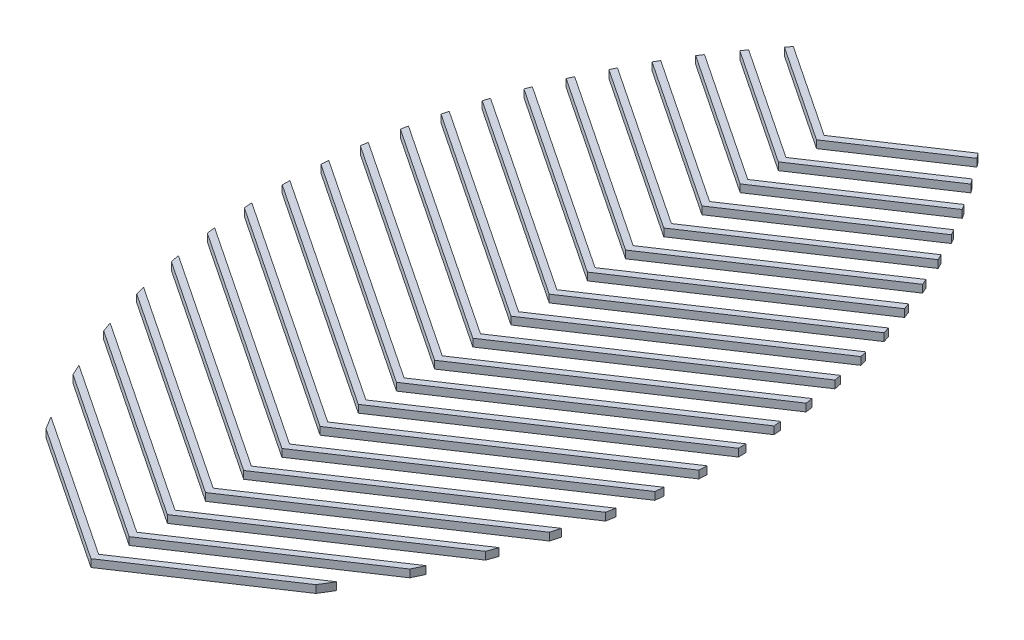
SolidWorks part; units mm, degrees
ref_plane "Front Plane" through (0, 0, 0) normal (0, 0, 1) x (1, 0, 0)
ref_plane "Top Plane" through (0, 0, 0) normal (0, 1, 0) x (1, 0, 0)
ref_plane "Right Plane" through (0, 0, 0) normal (1, 0, 0) x (0, 0, -1)
sketch "Sketch2" plane through (0, 0, 0) normal (0, 1, 0) x (1, 0, 0)
  line L0 (-15.0876, 6.8922) -> (8.6636, -8.942)
  line L1 (8.6636, -8.942) -> (32.4148, 6.8922)
  line L2 (-20.2008, 16.651) -> (8.6636, -2.592)
  line L3 (8.6636, -3.862) -> (8.6636, -8.942) construction
  line L4 (-13.7712, 4.7445) -> (8.6636, -10.212)
  line L5 (8.6636, -10.212) -> (31.0984, 4.7445)
  line L7 (8.6636, -8.942) -> (8.6636, -10.212) construction
  line L9 (8.6636, -2.592) -> (37.5281, 16.651)
  line L10 (-19.336, 14.8045) -> (8.6636, -3.862)
  line L11 (8.6636, -3.862) -> (36.6632, 14.8045)
  line L14 (8.6636, 2.488) -> (8.6636, -2.592) construction
  line L15 (8.6636, -2.592) -> (8.6636, -3.862) construction
  line L16 (-23.6775, 25.3188) -> (8.6636, 3.758)
  line L17 (8.6636, 3.758) -> (41.0047, 25.3188)
  line L18 (-23.0802, 23.6506) -> (8.6636, 2.488)
  line L19 (8.6636, 2.488) -> (40.4074, 23.6506)
  line L22 (8.6636, 8.838) -> (8.6636, 3.758) construction
  line L23 (8.6636, 3.758) -> (8.6636, 2.488) construction
  line L24 (-26.0837, 33.2729) -> (8.6636, 10.108)
  line L25 (8.6636, 10.108) -> (43.4109, 33.2729)
  line L26 (-25.6722, 31.7286) -> (8.6636, 8.838)
  line L27 (8.6636, 8.838) -> (42.9994, 31.7286)
  line L30 (8.6636, 15.188) -> (8.6636, 10.108) construction
  line L31 (8.6636, 10.108) -> (8.6636, 8.838) construction
  line L32 (-27.7036, 40.7028) -> (8.6636, 16.458)
  line L33 (8.6636, 16.458) -> (45.0308, 40.7028)
  line L34 (-27.4334, 39.2527) -> (8.6636, 15.188)
  line L35 (8.6636, 15.188) -> (44.7606, 39.2527)
  line L38 (8.6636, 21.538) -> (8.6636, 16.458) construction
  line L39 (8.6636, 16.458) -> (8.6636, 15.188) construction
  line L40 (-28.7043, 47.72) -> (8.6636, 22.808)
  line L41 (8.6636, 22.808) -> (46.0315, 47.72)
  line L42 (-28.5479, 46.3457) -> (8.6636, 21.538)
  line L43 (8.6636, 21.538) -> (45.8752, 46.3457)
  line L46 (8.6636, 27.888) -> (8.6636, 22.808) construction
  line L47 (8.6636, 22.808) -> (8.6636, 21.538) construction
  line L48 (-29.1937, 54.3963) -> (8.6636, 29.158)
  line L49 (8.6636, 29.158) -> (46.5209, 54.3963)
  line L50 (-29.1328, 53.0857) -> (8.6636, 27.888)
  line L51 (8.6636, 27.888) -> (46.4601, 53.0857)
  line L54 (8.6636, 34.238) -> (8.6636, 29.158) construction
  line L55 (8.6636, 29.158) -> (8.6636, 27.888) construction
  line L56 (-29.246, 60.7811) -> (8.6636, 35.508)
  line L57 (8.6636, 35.508) -> (46.5732, 60.7811)
  line L58 (-29.2677, 59.5256) -> (8.6636, 34.238)
  line L59 (8.6636, 34.238) -> (46.5949, 59.5256)
  line L62 (8.6636, 40.588) -> (8.6636, 35.508) construction
  line L63 (8.6636, 35.508) -> (8.6636, 34.238) construction
  line L64 (-28.9145, 66.9101) -> (8.6636, 41.858)
  line L65 (8.6636, 41.858) -> (46.2417, 66.9101)
  line L66 (-29.0094, 65.7034) -> (8.6636, 40.588)
  line L67 (8.6636, 40.588) -> (46.3367, 65.7034)
  line L70 (8.6636, 46.938) -> (8.6636, 41.858) construction
  line L71 (8.6636, 41.858) -> (8.6636, 40.588) construction
  line L72 (-28.2388, 72.8096) -> (8.6636, 48.208)
  line L73 (8.6636, 48.208) -> (45.566, 72.8096)
  line L74 (-28.3999, 71.647) -> (8.6636, 46.938)
  line L75 (8.6636, 46.938) -> (45.7271, 71.647)
  line L78 (8.6636, 53.288) -> (8.6636, 48.208) construction
  line L79 (8.6636, 48.208) -> (8.6636, 46.938) construction
  line L80 (-27.2489, 78.4997) -> (8.6636, 54.558)
  line L81 (8.6636, 54.558) -> (44.5761, 78.4997)
  line L82 (-27.4708, 77.3777) -> (8.6636, 53.288)
  line L83 (8.6636, 53.288) -> (44.798, 77.3777)
  line L86 (8.6636, 59.638) -> (8.6636, 54.558) construction
  line L87 (8.6636, 54.558) -> (8.6636, 53.288) construction
  line L88 (-25.968, 83.9958) -> (8.6636, 60.908)
  line L89 (8.6636, 60.908) -> (43.2952, 83.9958)
  line L90 (-26.2465, 82.9115) -> (8.6636, 59.638)
  line L91 (8.6636, 59.638) -> (43.5737, 82.9115)
  line L94 (8.6636, 65.988) -> (8.6636, 60.908) construction
  line L95 (8.6636, 60.908) -> (8.6636, 59.638) construction
  line L96 (-24.4139, 89.3097) -> (8.6636, 67.258)
  line L97 (8.6636, 67.258) -> (41.7411, 89.3097)
  line L98 (-24.7458, 88.261) -> (8.6636, 65.988)
  line L99 (8.6636, 65.988) -> (42.073, 88.261)
  line L102 (8.6636, 72.338) -> (8.6636, 67.258) construction
  line L103 (8.6636, 67.258) -> (8.6636, 65.988) construction
  line L104 (-22.6004, 94.4507) -> (8.6636, 73.608)
  line L105 (8.6636, 73.608) -> (39.9276, 94.4507)
  line L106 (-22.9833, 93.436) -> (8.6636, 72.338)
  line L107 (8.6636, 72.338) -> (40.3105, 93.436)
  line L110 (8.6636, 78.688) -> (8.6636, 73.608) construction
  line L111 (8.6636, 73.608) -> (8.6636, 72.338) construction
  line L112 (-20.5381, 99.4258) -> (8.6636, 79.958)
  line L113 (8.6636, 79.958) -> (37.8653, 99.4258)
  line L114 (-20.9701, 98.4438) -> (8.6636, 78.688)
  line L115 (8.6636, 78.688) -> (38.2973, 98.4438)
  line L118 (8.6636, 85.038) -> (8.6636, 79.958) construction
  line L119 (8.6636, 79.958) -> (8.6636, 78.688) construction
  line L120 (-18.2347, 104.2403) -> (8.6636, 86.308)
  line L121 (8.6636, 86.308) -> (35.562, 104.2403)
  line L122 (-18.7144, 103.29) -> (8.6636, 85.038)
  line L123 (8.6636, 85.038) -> (36.0416, 103.29)
  line L126 (8.6636, 91.388) -> (8.6636, 86.308) construction
  line L127 (8.6636, 86.308) -> (8.6636, 85.038) construction
  line L128 (-15.6958, 108.8976) -> (8.6636, 92.658)
  line L129 (8.6636, 92.658) -> (33.023, 108.8976)
  line L130 (-16.2222, 107.9786) -> (8.6636, 91.388)
  line L131 (8.6636, 91.388) -> (33.5494, 107.9786)
  line L134 (8.6636, 97.738) -> (8.6636, 92.658) construction
  line L135 (8.6636, 92.658) -> (8.6636, 91.388) construction
  line L136 (-12.9245, 113.4001) -> (8.6636, 99.008)
  line L137 (8.6636, 99.008) -> (30.2517, 113.4001)
  line L138 (-13.4973, 112.512) -> (8.6636, 97.738)
  line L139 (8.6636, 97.738) -> (30.8245, 112.512)
  line L142 (8.6636, 104.088) -> (8.6636, 99.008) construction
  line L143 (8.6636, 99.008) -> (8.6636, 97.738) construction
  line L144 (-9.9223, 117.7486) -> (8.6636, 105.358)
  line L145 (8.6636, 105.358) -> (27.2495, 117.7486)
  line L146 (-10.5412, 116.8912) -> (8.6636, 104.088)
  line L147 (8.6636, 104.088) -> (27.8684, 116.8912)
  line L150 (8.6636, 110.438) -> (8.6636, 105.358) construction
  line L151 (8.6636, 105.358) -> (8.6636, 104.088) construction
  line L152 (-6.6885, 121.9428) -> (8.6636, 111.708)
  line L153 (8.6636, 111.708) -> (24.0157, 121.9428)
  line L154 (-7.3538, 121.1163) -> (8.6636, 110.438)
  line L155 (8.6636, 110.438) -> (24.6811, 121.1163)
  line L158 (8.6636, 116.788) -> (8.6636, 111.708) construction
  line L159 (8.6636, 111.708) -> (8.6636, 110.438) construction
  arc A0 (-6.6885, 121.9428) -> (-7.3538, 121.1163) centre (71.3713, 58.4122) ccw
  arc A1 (24.0157, 121.9428) -> (24.6811, 121.1163) centre (-54.0441, 58.4122) cw
  arc A2 (32.4148, 6.8922) -> (31.0984, 4.7445) centre (-54.0441, 58.4122) cw
  arc A3 (37.5281, 16.651) -> (36.6632, 14.8045) centre (-54.0441, 58.4122) cw
  arc A4 (41.0047, 25.3188) -> (40.4074, 23.6506) centre (-54.0441, 58.4122) cw
  arc A5 (43.4109, 33.2729) -> (42.9994, 31.7286) centre (-54.0441, 58.4122) cw
  arc A6 (45.0308, 40.7028) -> (44.7606, 39.2527) centre (-54.0441, 58.4122) cw
  arc A7 (46.0315, 47.72) -> (45.8752, 46.3457) centre (-54.0441, 58.4122) cw
  arc A8 (46.5209, 54.3963) -> (46.4601, 53.0857) centre (-54.0441, 58.4122) cw
  arc A9 (46.5732, 60.7811) -> (46.5949, 59.5256) centre (-54.0441, 58.4122) cw
  arc A10 (46.2417, 66.9101) -> (46.3367, 65.7034) centre (-54.0441, 58.4122) cw
  arc A11 (45.566, 72.8096) -> (45.7271, 71.647) centre (-54.0441, 58.4122) cw
  arc A12 (44.5761, 78.4997) -> (44.798, 77.3777) centre (-54.0441, 58.4122) cw
  arc A13 (43.2952, 83.9958) -> (43.5737, 82.9115) centre (-54.0441, 58.4122) cw
  arc A14 (41.7411, 89.3097) -> (42.073, 88.261) centre (-54.0441, 58.4122) cw
  arc A15 (39.9276, 94.4507) -> (40.3105, 93.436) centre (-54.0441, 58.4122) cw
  arc A16 (37.8653, 99.4258) -> (38.2973, 98.4438) centre (-54.0441, 58.4122) cw
  arc A17 (35.562, 104.2403) -> (36.0416, 103.29) centre (-54.0441, 58.4122) cw
  arc A18 (33.023, 108.8976) -> (33.5494, 107.9786) centre (-54.0441, 58.4122) cw
  arc A19 (30.2517, 113.4001) -> (30.8245, 112.512) centre (-54.0441, 58.4122) cw
  arc A20 (27.2495, 117.7486) -> (27.8684, 116.8912) centre (-54.0441, 58.4122) cw
  arc A21 (-15.0876, 6.8922) -> (-13.7712, 4.7445) centre (71.3713, 58.4122) ccw
  arc A22 (-23.6775, 25.3188) -> (-23.0802, 23.6506) centre (71.3713, 58.4122) ccw
  arc A23 (-20.2008, 16.651) -> (-19.336, 14.8045) centre (71.3713, 58.4122) ccw
  arc A24 (-26.0837, 33.2729) -> (-25.6722, 31.7286) centre (71.3713, 58.4122) ccw
  arc A25 (-27.7036, 40.7028) -> (-27.4334, 39.2527) centre (71.3713, 58.4122) ccw
  arc A26 (-28.7043, 47.72) -> (-28.5479, 46.3457) centre (71.3713, 58.4122) ccw
  arc A27 (-29.1937, 54.3963) -> (-29.1328, 53.0857) centre (71.3713, 58.4122) ccw
  arc A28 (-29.246, 60.7811) -> (-29.2677, 59.5256) centre (71.3713, 58.4122) ccw
  arc A29 (-28.9145, 66.9101) -> (-29.0094, 65.7034) centre (71.3713, 58.4122) ccw
  arc A30 (-28.2388, 72.8096) -> (-28.3999, 71.647) centre (71.3713, 58.4122) ccw
  arc A31 (-27.2489, 78.4997) -> (-27.4708, 77.3777) centre (71.3713, 58.4122) ccw
  arc A32 (-25.968, 83.9958) -> (-26.2465, 82.9115) centre (71.3713, 58.4122) ccw
  arc A33 (-24.4139, 89.3097) -> (-24.7458, 88.261) centre (71.3713, 58.4122) ccw
  arc A34 (-22.6004, 94.4507) -> (-22.9833, 93.436) centre (71.3713, 58.4122) ccw
  arc A35 (-20.5381, 99.4258) -> (-20.9701, 98.4438) centre (71.3713, 58.4122) ccw
  arc A36 (-18.2347, 104.2403) -> (-18.7144, 103.29) centre (71.3713, 58.4122) ccw
  arc A37 (-15.6958, 108.8976) -> (-16.2222, 107.9786) centre (71.3713, 58.4122) ccw
  arc A38 (-12.9245, 113.4001) -> (-13.4973, 112.512) centre (71.3713, 58.4122) ccw
  arc A39 (-9.9223, 117.7486) -> (-10.5412, 116.8912) centre (71.3713, 58.4122) ccw
  dimension "D1" = 1.27
  dimension "D3" = 20
extrude "Boss-Extrude1" add sketch "Sketch2" along normal blind 1.27
scale "Scale1" bodies to scale 120 112 113 111 109 108 106 114 107 118 104 115 101 119 105 116 102 117 110 103 scale about origin uniform scaling yes scale factor 1.5
